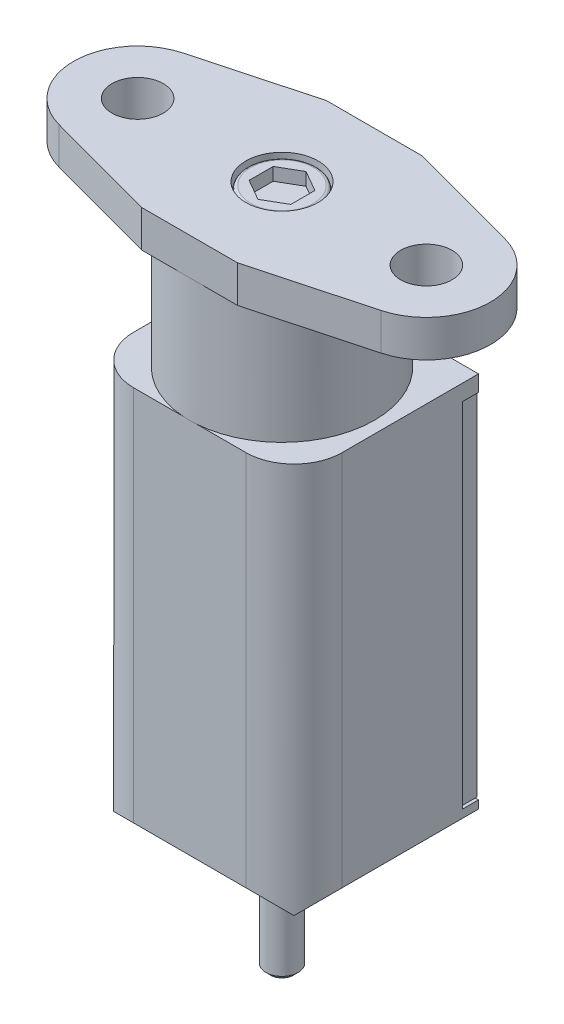
SolidWorks part; units mm, degrees
ref_plane "Front Plane" through (0, 0, 0) normal (0, 0, 1) x (1, 0, 0)
ref_plane "Top Plane" through (0, 0, 0) normal (0, 1, 0) x (1, 0, 0)
ref_plane "Right Plane" through (0, 0, 0) normal (1, 0, 0) x (0, 0, -1)
sketch "Sketch1" plane through (0, 0, 0) normal (0, 1, 0) x (1, 0, 0)
  line L0 (3, 5.765) -> (-3, 5.765)
  line L1 (-3, 5.765) -> (-10.0436, 3.8615)
  line L2 (3, -5.765) -> (10.0436, -3.8615)
  line L3 (3, -5.765) -> (-3, -5.765)
  line L4 (-3, -5.765) -> (-10.0436, -3.8615)
  line L5 (3, 5.765) -> (10.0436, 3.8615)
  line L6 (0, 5.765) -> (0, -5.765) construction
  line L7 (-13, 0) -> (13, 0) construction
  arc A0 (-10.0436, 3.8615) -> (-10.0436, -3.8615) centre (-9, 0) ccw
  arc A1 (10.0436, 3.8615) -> (10.0436, -3.8615) centre (9, 0) cw
  circle A2 centre (9, 0) radius 1.6
  circle A3 centre (-9, 0) radius 1.6
  point P2 (-13, 0)
  point P4 (13, 0)
  point P15 (0, 0)
  dimension "D3" = 4
  dimension "D4" = 9
  dimension "D6" = 3.2
  dimension "D1" = 6
  dimension "D2" = 5.765
  dimension "D5" = 26
extrude "Boss-Extrude1" add sketch "Sketch1" against normal blind 2.3
sketch "Sketch2" plane through (0, -2.3, 0) normal (0, -1, 0) x (1, 0, 0)
  circle A0 centre (0, 0) radius 5.765
extrude "Boss-Extrude2" add sketch "Sketch2" along normal blind 7.7
ref_plane "Plane1" through (0, 0, 0) normal (0, 0, 1) x (1, 0, 0)
sketch "Sketch3" plane through (0, 0, 0) normal (0, 0, 1) x (1, 0, 0)
  line L0 (-6.5, -10) -> (6.5, -10)
  line L1 (-6.5, -10) -> (-6.5, -36.5)
  line L2 (-6.5, -36.5) -> (6.5, -36.5)
  line L3 (6.5, -36.5) -> (6.5, -10)
  line L5 (-5.765, -10) -> (5.765, -10) construction
  line L6 (0, 0) -> (0, -10) construction
  dimension "D1" = 6.5
  dimension "D2" = 26.5
extrude "Boss-Extrude3" add sketch "Sketch3" against normal blind 5.75 and the other way blind 5.75
ref_plane "Plane2" through (0, 0, 0) normal (0, 0, 1) x (1, 0, 0)
sketch "Sketch4" plane through (0, 0, 0) normal (0, 0, 1) x (1, 0, 0)
  line L0 (1, -36.5) -> (0, -36.5)
  line L1 (0, -36.5) -> (0, -42.5)
  line L2 (0, -42.5) -> (1, -42.5)
  line L3 (1, -42.5) -> (1, -36.5)
  line L4 (0, -36.5) -> (0, -42.5) construction
  line L5 (-6.5, -36.5) -> (6.5, -36.5) construction
  point P7 (0, -36.5)
  dimension "D1" = 6
  dimension "D2" = 1
revolve "Revolve1" add sketch "Sketch4" angle 360 about L4
chamfer "Chamfer1" distance 3 angle 45 4 edges at (6.5, -36.5, 0) (0, -36.5, 5.75) (0, -36.5, -5.75) (-6.5, -36.5, 0)
fillet "Fillet1" radius 3 2 edges at (6.5, -21.75, 5.75) (-6.5, -21.75, 5.75)
chamfer "Chamfer2" distance 0.3 angle 45 1 edges at (1, -42.5, 0)
sketch "Sketch9" plane through (0, 0, 0) normal (0, 1, 0) x (1, 0, 0)
  line L1 (0, 1.5011) -> (-1.3, 0.7506)
  line L2 (-1.3, 0.7506) -> (-1.3, -0.7506)
  line L3 (-1.3, -0.7506) -> (0, -1.5011)
  line L4 (0, -1.5011) -> (1.3, -0.7506)
  line L5 (1.3, -0.7506) -> (1.3, 0.7506)
  line L6 (1.3, 0.7506) -> (0, 1.5011)
  circle A0 centre (0, 0) radius 2.25
  circle A1 centre (0, 0) radius 1.3 construction
  dimension "D1" = 4.5
  dimension "D2" = 2.6
extrude "Cut-Extrude1" cut sketch "Sketch9" against normal blind 0.2
sketch "Sketch10" plane through (0, 0, 0) normal (0, 1, 0) x (1, 0, 0)
  line L6 (1.3, 0.7506) -> (0, 1.5011)
  line L7 (0, 1.5011) -> (-1.3, 0.7506)
  line L8 (-1.3, 0.7506) -> (-1.3, -0.7506)
  line L9 (-1.3, -0.7506) -> (0, -1.5011)
  line L10 (0, -1.5011) -> (1.3, -0.7506)
  line L11 (1.3, -0.7506) -> (1.3, 0.7506)
  line L12 (1.3, 0.7506) -> (0, 1.5011)
  line L13 (0, 1.5011) -> (-1.3, 0.7506)
  line L14 (-1.3, 0.7506) -> (-1.3, -0.7506)
  line L15 (-1.3, -0.7506) -> (0, -1.5011)
  line L16 (0, -1.5011) -> (1.3, -0.7506)
  line L17 (1.3, -0.7506) -> (1.3, 0.7506)
  dimension "D1" = 0
extrude "Cut-Extrude2" cut sketch "Sketch10" against normal blind 1
sketch "Sketch11" plane through (0, -0.2, 0) normal (0, 1, 0) x (1, 0, 0)
  circle A0 centre (0, 0) radius 2.15
  circle A1 centre (0, 0) radius 2.25
  circle A2 centre (0, 0) radius 2.25
  dimension "D1" = 0
  dimension "D2" = 0.1
extrude "Cut-Extrude3" cut sketch "Sketch11" against normal blind 0.5
fillet "Fillet2" radius 0.2 1 edges at (0, -0.2, 2.15)
sketch "Sketch12" plane through (0, 0, -5.75) normal (0, 0, -1) x (-1, 0, 0)
  line L0 (-6.5, -10) -> (-6.5, -11) construction
  line L1 (0, -33.5) -> (0, -32.5) construction
  line L2 (-6.5, -11) -> (6.5, -11)
  line L3 (-6.5, -11) -> (-6.5, -33)
  line L4 (-6.5, -33) -> (-1, -33)
  line L5 (6.5, -11) -> (6.5, -33)
  line L6 (-1, -32.5) -> (-1, -33)
  line L7 (1, -32.5) -> (1, -33)
  line L8 (1, -33) -> (6.5, -33)
  line L9 (-6.5, -33.5) -> (6.5, -33.5) construction
  arc A0 (-1, -32.5) -> (1, -32.5) centre (0, -32.5) cw
  circle A1 centre (0, -32.5) radius 0.3
  dimension "D3" = 1
  dimension "D4" = 0.6
  dimension "D1" = 1
  dimension "D2" = 1
  dimension "D5" = 0.5
extrude "Cut-Extrude4" cut sketch "Sketch12" against normal blind 1
sketch "Sketch13" plane through (0, 0, -4.75) normal (0, 0, -1) x (-1, 0, 0)
  line L0 (6.4, -11.1) -> (-6.4, -11.1)
  line L1 (-6.4, -11.1) -> (-6.4, -32.9)
  line L2 (-6.4, -32.9) -> (-1.1, -32.9)
  line L3 (-1.1, -32.9) -> (-1.1, -32.5)
  line L4 (1.1, -32.5) -> (1.1, -32.9)
  line L5 (1.1, -32.9) -> (6.4, -32.9)
  line L6 (6.4, -32.9) -> (6.4, -11.1)
  line L7 (-6.5, -11) -> (-6.5, -33)
  line L8 (-6.5, -33) -> (-1, -33)
  line L9 (-1, -33) -> (-1, -32.5)
  line L10 (1, -32.5) -> (1, -33)
  line L11 (1, -33) -> (6.5, -33)
  line L12 (6.5, -33) -> (6.5, -11)
  line L13 (6.5, -11) -> (-6.5, -11)
  line L14 (-6.5, -11) -> (-6.5, -33) construction
  line L15 (-6.5, -33) -> (-1, -33) construction
  line L16 (-1, -33) -> (-1, -32.5) construction
  line L17 (1, -32.5) -> (1, -33) construction
  line L18 (1, -33) -> (6.5, -33) construction
  line L19 (6.5, -33) -> (6.5, -11) construction
  line L20 (6.5, -11) -> (-6.5, -11) construction
  arc A0 (1.1, -32.5) -> (-1.1, -32.5) centre (0, -32.5) ccw
  arc A1 (1, -32.5) -> (-1, -32.5) centre (0, -32.5) ccw
  arc A2 (1, -32.5) -> (-1, -32.5) centre (0, -32.5) ccw construction
  dimension "D1" = 0
  dimension "D2" = 0.1
extrude "Boss-Extrude4" add sketch "Sketch13" along normal blind 1
